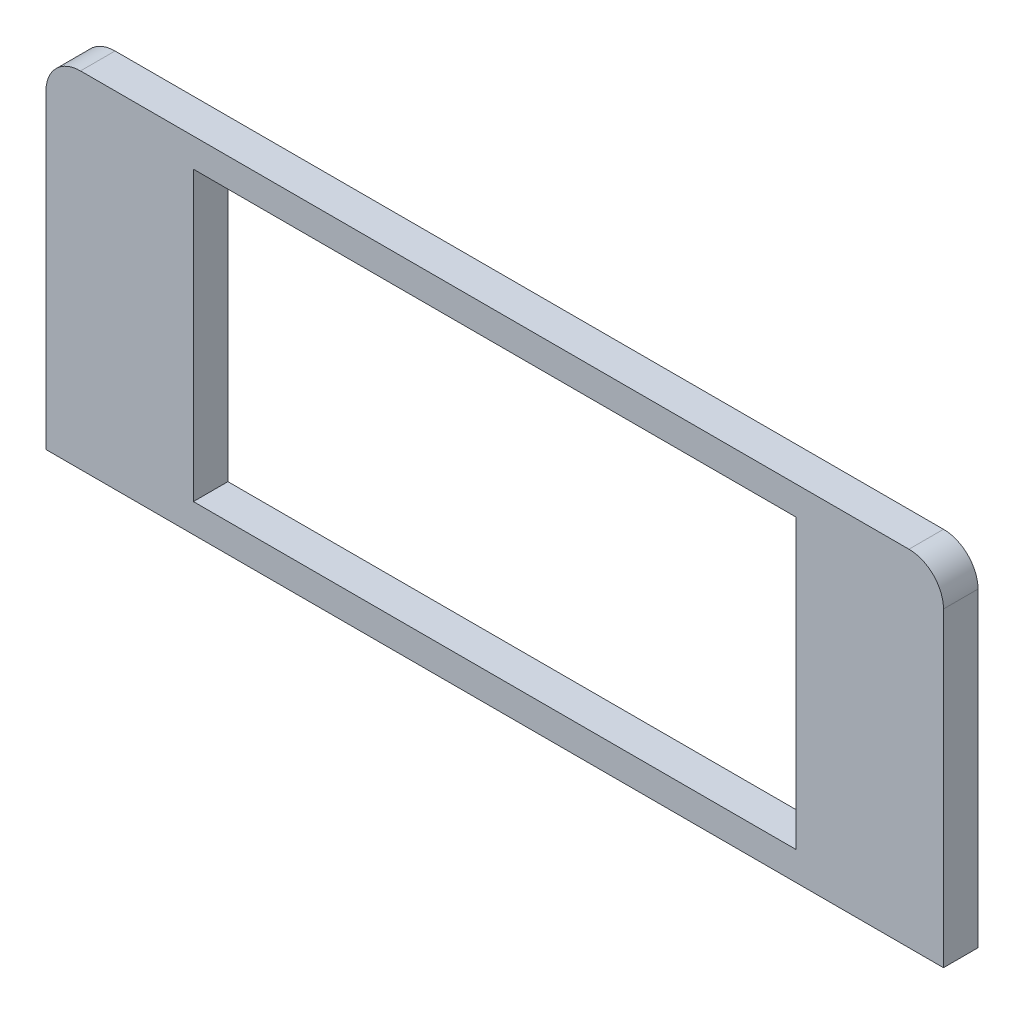
SolidWorks part; units mm, degrees
ref_plane "Front Plane" through (0, 0, 0) normal (0, 0, 1) x (1, 0, 0)
ref_plane "Top Plane" through (0, 0, 0) normal (0, 1, 0) x (1, 0, 0)
ref_plane "Right Plane" through (0, 0, 0) normal (1, 0, 0) x (0, 0, -1)
sketch "Sketch1" plane through (0, 0, 0) normal (0, 0, 1) x (1, 0, 0)
  line L1 (-65, 25) -> (65, 25)
  line L2 (-65, 25) -> (-65, -25)
  line L3 (-65, -25) -> (65, -25)
  line L4 (65, 25) -> (65, -25)
  line L5 (-65, 25) -> (65, -25) construction
  line L6 (-65, -25) -> (65, 25) construction
  point P0 (0, 0)
  dimension "D1" = 130
  dimension "D2" = 50
extrude "Boss-Extrude1" add sketch "Sketch1" along normal blind 5
fillet "Fillet1" radius 5 2 edges at (65, 25, 2.5) (-65, 25, 2.5)
sketch "Sketch2" plane through (0, 0, 5) normal (0, 0, 1) x (1, 0, 0)
  line L1 (-43.65, 20.85) -> (43.65, 20.85)
  line L2 (-43.65, 20.85) -> (-43.65, -20.85)
  line L3 (-43.65, -20.85) -> (43.65, -20.85)
  line L4 (43.65, 20.85) -> (43.65, -20.85)
  line L5 (-43.65, 20.85) -> (43.65, -20.85) construction
  line L6 (-43.65, -20.85) -> (43.65, 20.85) construction
  point P0 (0, 0)
  dimension "D1" = 87.3
  dimension "D2" = 41.7
extrude "Cut-Extrude1" cut sketch "Sketch2" against normal blind 5 contours L2 L1 L4 L3
